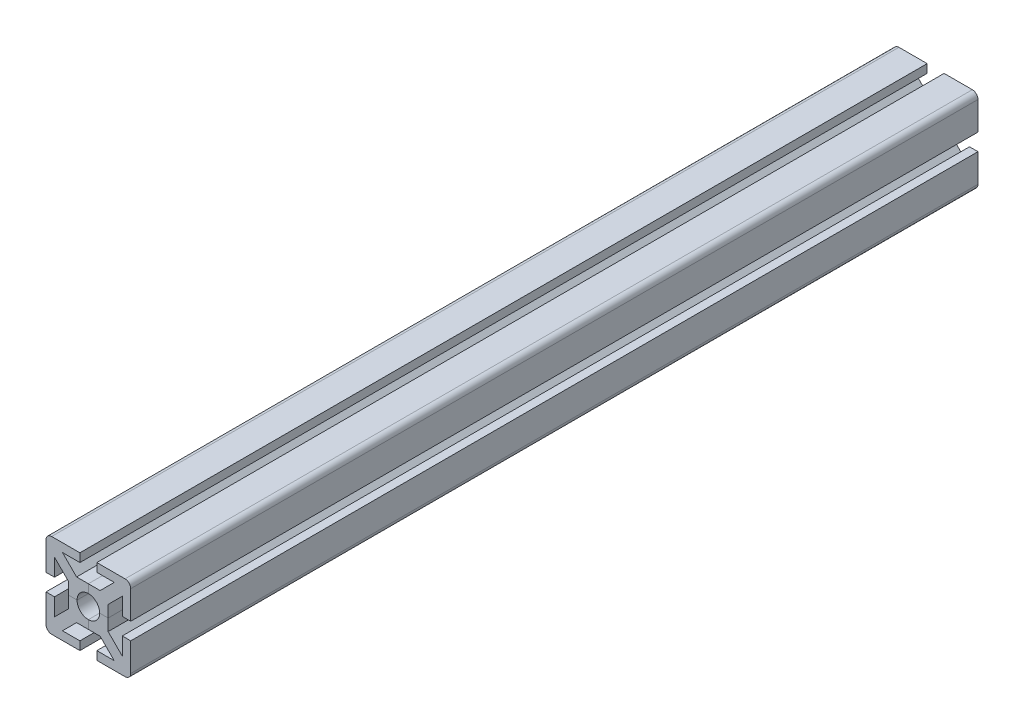
SolidWorks part; units mm, degrees
ref_plane "Alzado" through (0, 0, 0) normal (0, 0, 1) x (1, 0, 0)
ref_plane "Planta" through (0, 0, 0) normal (0, 1, 0) x (1, 0, 0)
ref_plane "Vista lateral" through (0, 0, 0) normal (1, 0, 0) x (0, 0, -1)
sketch "Croquis1" plane through (0, 0, 0) normal (0, 0, 1) x (1, 0, 0)
  line L0 (0, 0) -> (50000, 0) construction
  line L1 (-15, 15) -> (15, 15) construction
  line L2 (-15, 15) -> (-15, -15) construction
  line L3 (-15, -15) -> (15, -15) construction
  line L4 (15, 15) -> (15, -15) construction
  line L5 (-15, 15) -> (15, -15) construction
  line L6 (-15, -15) -> (15, 15) construction
  line L7 (0, 0) -> (0, -50000) construction
  line L8 (0, 4) -> (0, 7)
  line L9 (0, 7) -> (4.1716, 7)
  line L10 (4.1716, 7) -> (9.1716, 12)
  line L11 (9.1716, 12) -> (3, 12)
  line L12 (3, 12) -> (3, 15)
  line L13 (3, 15) -> (15, 15)
  line L20 (2.8284, 2.8284) -> (15, 15)
  arc A0 (2.8284, 2.8284) -> (0, 4) centre (0, 0) ccw
  point P0 (0, 0)
  dimension "D3" = 4
  dimension "D1" = 30
  dimension "D2" = 6
  dimension "D4" = 8
  dimension "D5" = 3
  dimension "D6" = 2
extrude "Saliente-Extruir1" add sketch "Croquis1" along normal mid plane 300
mirror "Simetría1" about plane through (2.8284, 2.8284, 150) normal (-0.7071, 0.7071, 0) of "Saliente-Extruir1"
fillet "Redondeo1" radius 2 1 edges at (15, 15, 0)
pattern_circular "MatrizC4" count 4 over 360 about axis through (0, 0, 0) along (0, 0, 1) of bodies 102
